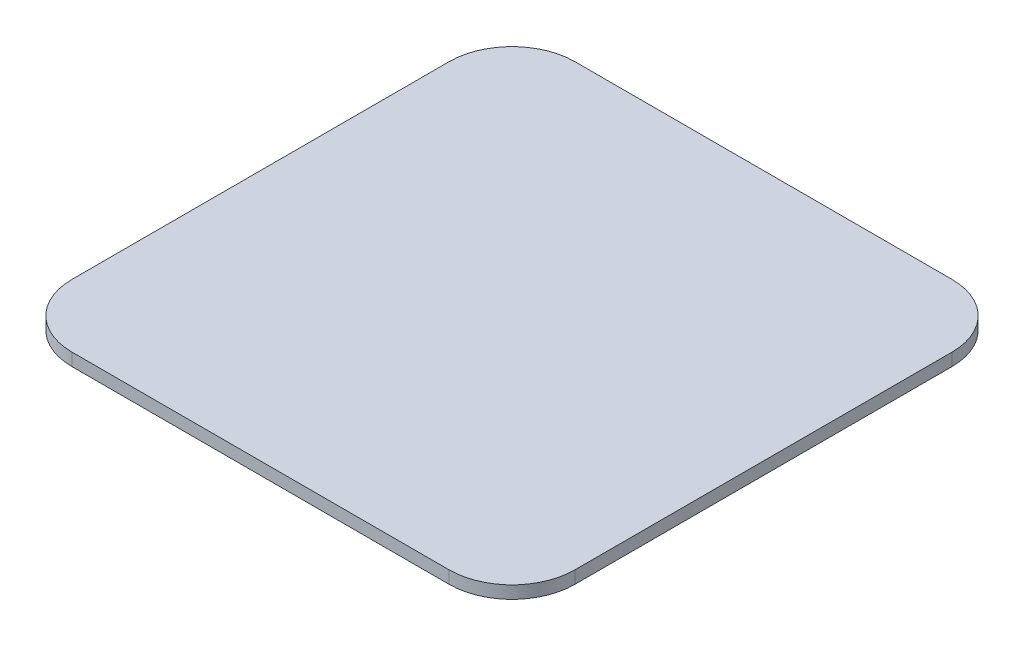
SolidWorks part; units mm, degrees
ref_plane "前视基准面" through (0, 0, 0) normal (0, 0, 1) x (1, 0, 0)
ref_plane "上视基准面" through (0, 0, 0) normal (0, 1, 0) x (1, 0, 0)
ref_plane "右视基准面" through (0, 0, 0) normal (1, 0, 0) x (0, 0, -1)
sketch "草图1" plane through (0, 0, 0) normal (0, 1, 0) x (1, 0, 0)
  line L0 (0, -55) -> (0, 55) construction
  line L1 (-15, 20) -> (15, 20)
  line L2 (-20, 15) -> (-20, -15)
  line L3 (-15, -20) -> (15, -20)
  line L4 (20, 15) -> (20, -15)
  line L5 (-55, 0) -> (55, 0) construction
  arc A0 (-20, -15) -> (-15, -20) centre (-15, -15) ccw
  arc A1 (15, -20) -> (20, -15) centre (15, -15) ccw
  arc A2 (20, 15) -> (15, 20) centre (15, 15) ccw
  arc A3 (-20, 15) -> (-15, 20) centre (-15, 15) cw
  dimension "D5" = 5
  dimension "D1" = 20
  dimension "D2" = 20
  dimension "D3" = 20
  dimension "D4" = 20
extrude "凸台-拉伸1" add sketch "草图1" along normal blind 1
